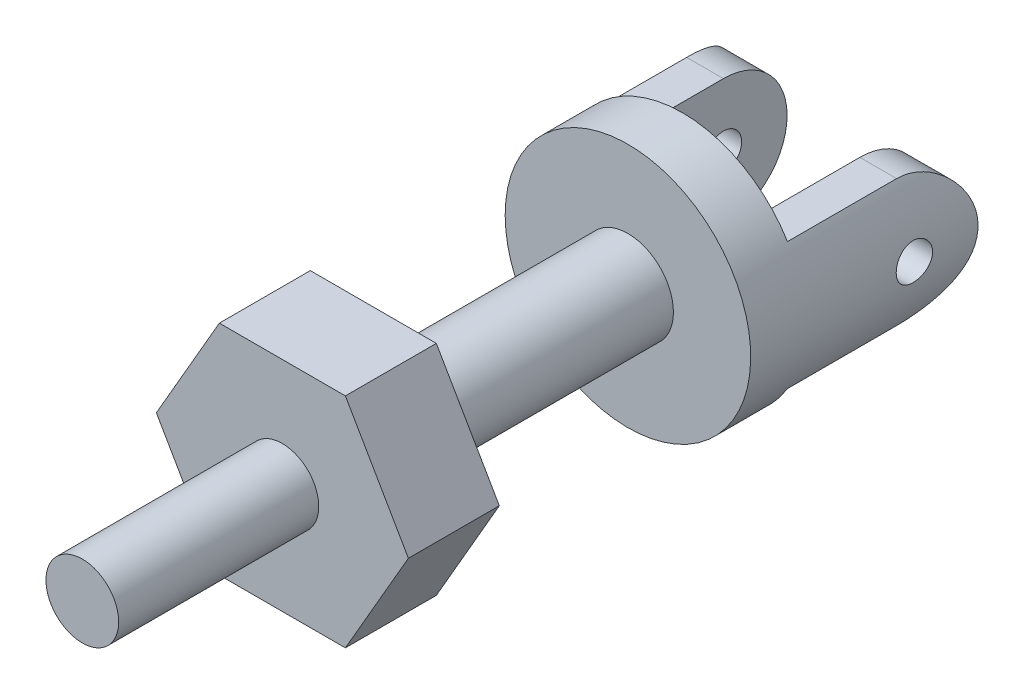
SolidWorks part; units mm, degrees
ref_plane "Front Plane" through (0, 0, 0) normal (0, 0, 1) x (1, 0, 0)
ref_plane "Top Plane" through (0, 0, 0) normal (0, 1, 0) x (1, 0, 0)
ref_plane "Right Plane" through (0, 0, 0) normal (1, 0, 0) x (0, 0, -1)
sketch "Sketch2" plane through (0, 0, 0) normal (0, 0, 1) x (1, 0, 0)
  line L1 (3.4641, -6) -> (6.9282, 0)
  line L2 (6.9282, 0) -> (3.4641, 6)
  line L3 (3.4641, 6) -> (-3.4641, 6)
  line L4 (-3.4641, 6) -> (-6.9282, 0)
  line L5 (-6.9282, 0) -> (-3.4641, -6)
  line L6 (-3.4641, -6) -> (3.4641, -6)
  circle A0 centre (0, 0) radius 6 construction
  dimension "D1" = 12
extrude "Hexagon" add sketch "Sketch2" along normal blind 5
sketch "Sketch3" plane through (0, 0, 5) normal (0, 0, 1) x (1, 0, 0)
  circle A0 centre (0, 0) radius 2
  dimension "D1" = 4
extrude "Screw Post" add sketch "Sketch3" along normal blind 11
sketch "Sketch4" plane through (0, 0, 0) normal (0, 0, -1) x (-1, 0, 0)
  circle A0 centre (0, 0) radius 2.5
  dimension "D1" = 5
extrude "Bearing Section" add sketch "Sketch4" along normal blind 14
sketch "Sketch5" plane through (0, 0, -14) normal (0, 0, -1) x (-1, 0, 0)
  circle A0 centre (0, 0) radius 6.75
  dimension "D1" = 13.5
extrude "U Joint Base" add sketch "Sketch5" along normal blind 3
sketch "Sketch6" plane through (0, 0, -17) normal (0, 0, -1) x (-1, 0, 0)
  line L0 (-5.7717, 3.5) -> (-3.75, 3.5)
  line L1 (-3.75, 3.5) -> (-3.75, -3.5)
  line L2 (-3.75, -3.5) -> (-5.7717, -3.5)
  line L3 (3.75, -3.5) -> (3.75, 3.5)
  line L4 (3.75, 3.5) -> (5.7717, 3.5)
  line L5 (5.7717, -3.5) -> (3.75, -3.5)
  circle A0 centre (0, 0) radius 6.75 construction
  arc A1 (-5.7717, 3.5) -> (-5.7717, -3.5) centre (0, 0) ccw
  arc A2 (5.7717, -3.5) -> (5.7717, 3.5) centre (0, 0) ccw
  point P16 (0, 0)
  dimension "D2" = 7.5
  dimension "D3" = 7
  dimension "D1" = 2
extrude "U Joint Standups" add sketch "Sketch6" along normal blind 9.5
sketch "Sketch7" plane through (0, 0, 0) normal (1, 0, 0) x (0, 0, -1)
  line L0 (23, 3.5) -> (26.5, 3.5)
  line L1 (26.5, 3.5) -> (17, 3.5) construction
  line L2 (26.5, 3.5) -> (26.5, -3.5)
  line L4 (-5, 0) -> (0, 0) construction
  line L5 (23, -3.5) -> (26.5, -3.5)
  arc A0 (23, -3.5) -> (23, 3.5) centre (23, 0) ccw
extrude "Standup Round" cut sketch "Sketch7" against normal through all both and the other way through all contours A0 L5 L2 | A0 L2 L0
sketch "Sketch8" plane through (0, 0, 0) normal (1, 0, 0) x (0, 0, -1)
  circle A0 centre (23, 0) radius 1
  arc A1 (23, -3.5) -> (23, 3.5) centre (23, 0) ccw construction
  dimension "D1" = 2
extrude "Ball Holes" cut sketch "Sketch8" against normal through all both and the other way through all
